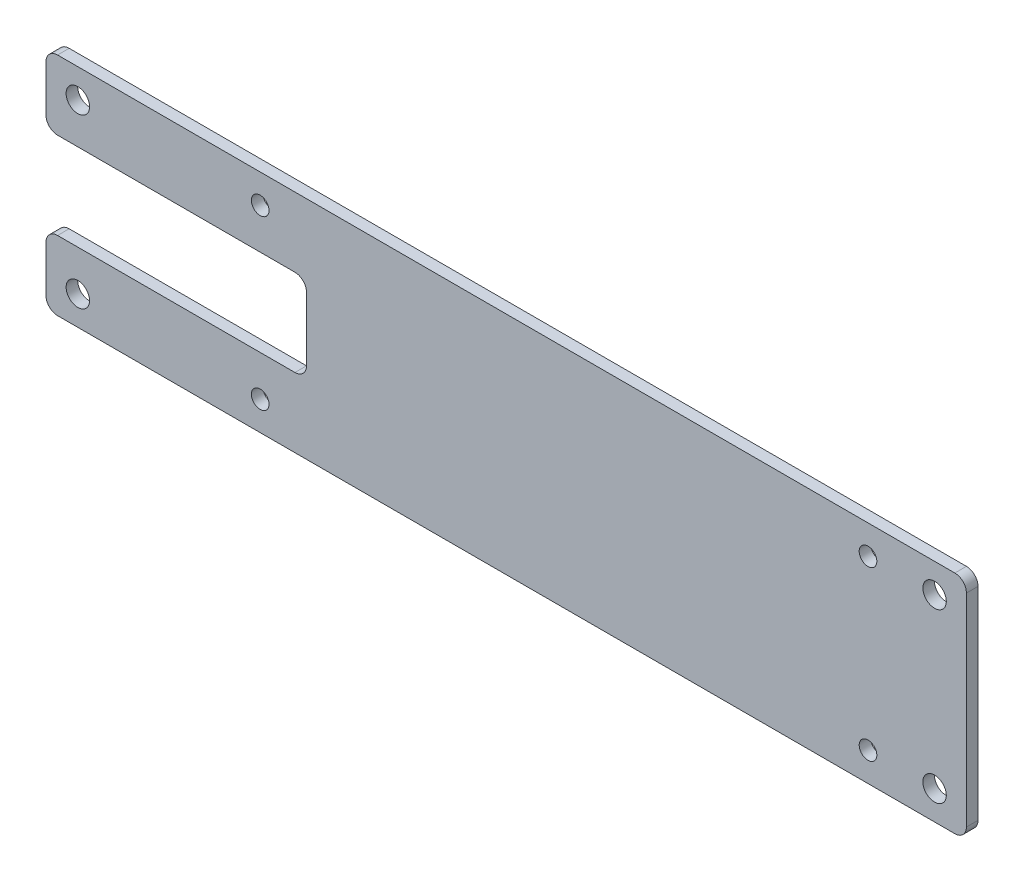
SolidWorks part; units mm, degrees
material "环氧树脂,未充填"
ref_plane "前视基准面" through (0, 0, 0) normal (0, 0, 1) x (1, 0, 0)
ref_plane "上视基准面" through (0, 0, 0) normal (0, 1, 0) x (1, 0, 0)
ref_plane "右视基准面" through (0, 0, 0) normal (1, 0, 0) x (0, 0, -1)
other "Configuration Table"
sketch "草图1" plane through (0, 0, 0) normal (0, 0, 1) x (1, 0, 0)
  line L0 (-57.5, -19.5) -> (-57.5, 19.5)
  line L1 (-52.5, -14.5) -> (52.5, -14.5) construction
  line L2 (-52.5, -14.5) -> (-52.5, 14.5) construction
  line L3 (-52.5, 14.5) -> (52.5, 14.5) construction
  line L4 (52.5, -14.5) -> (52.5, 14.5) construction
  line L5 (-52.5, -14.5) -> (52.5, 14.5) construction
  line L6 (-52.5, 14.5) -> (52.5, -14.5) construction
  line L7 (-57.5, 19.5) -> (57.5, 19.5)
  line L8 (57.5, -19.5) -> (57.5, 19.5)
  line L9 (-57.5, -19.5) -> (57.5, -19.5)
  line L10 (0, 0) -> (50000, 0) construction
  line L12 (69.5, -19.5) -> (-89.5, -19.5)
  line L13 (69.5, -19.5) -> (69.5, 19.5)
  line L14 (69.5, 19.5) -> (-89.5, 19.5)
  line L15 (-89.5, -19.5) -> (-89.5, 19.5)
  line L16 (69.5, -19.5) -> (-89.5, 19.5) construction
  line L17 (69.5, 19.5) -> (-89.5, -19.5) construction
  line L18 (64, -14.5) -> (-84, -14.5) construction
  line L19 (64, -14.5) -> (64, 14.5) construction
  line L20 (64, 14.5) -> (-84, 14.5) construction
  line L21 (-84, -14.5) -> (-84, 14.5) construction
  line L22 (64, -14.5) -> (-84, 14.5) construction
  line L23 (64, 14.5) -> (-84, -14.5) construction
  circle A0 centre (-52.5, 14.5) radius 1.525
  circle A1 centre (-52.5, -14.5) radius 1.525
  circle A2 centre (52.5, -14.5) radius 1.525
  circle A3 centre (52.5, 14.5) radius 1.525
  circle A4 centre (-84, 14.5) radius 2.025
  circle A5 centre (-84, -14.5) radius 2.025
  circle A6 centre (64, 14.5) radius 2.025
  circle A7 centre (64, -14.5) radius 2.025
  point P0 (0, 0)
  point P16 (-10, 0)
  point P22 (-10, 0)
  dimension "D4" = 3.05
  dimension "D5" = 4.05
  dimension "D6" = 5.5
  dimension "D1" = 105
  dimension "D2" = 29
  dimension "D7" = 148
  dimension "D8" = 29
  dimension "D9" = 10
  dimension "D3" = 5
extrude "凸台-拉伸1" add sketch "草图1" along normal blind 2 contours L15 L12 L0 L14 A5 A4 | L0 L9 L8 L7 A3 A2 A1 A0 | L13 L14 L8 L12 A7 A6
sketch "草图2" plane through (0, 0, 2) normal (0, 0, 1) x (1, 0, 0)
  line L0 (-84, 14.5) -> (-57.5, 14.5) construction
  line L1 (-57.5, 14.5) -> (-57.5, 0) construction
  line L2 (-57.5, 0) -> (0, 0) construction
  line L3 (-89.5, -19.5) -> (-89.5, 19.5) construction
  line L4 (-70.5, -7.5) -> (-44.5, -7.5)
  line L5 (-70.5, -7.5) -> (-70.5, 7.5)
  line L6 (-70.5, 7.5) -> (-44.5, 7.5)
  line L7 (-44.5, -7.5) -> (-44.5, 7.5)
  line L8 (-70.5, -7.5) -> (-44.5, 7.5) construction
  line L9 (-70.5, 7.5) -> (-44.5, -7.5) construction
  line L10 (-70.5, 7.5) -> (-89.5, 7.5)
  line L11 (-70.5, 7.5) -> (-70.5, -7.5)
  line L12 (-70.5, -7.5) -> (-89.5, -7.5)
  line L13 (-89.5, 7.5) -> (-89.5, -7.5)
  line M3 (-89.5, 19.5) -> (-89.5, -19.5)
  dimension "D1" = 26.5
  dimension "D2" = 15
  dimension "D3" = 26
extrude "切除-拉伸1" cut sketch "草图2" against normal blind 10 contours L12 L5 L10 M3 | L4 L7 L6 L5
fillet "圆角1" radius 2 8 edges at (-89.5, -7.5, 1) (-89.5, -19.5, 1) (69.5, -19.5, 1) (69.5, 19.5, 1) (-89.5, 19.5, 1) (-89.5, 7.5, 1) (-44.5, -7.5, 1) (-44.5, 7.5, 1)
